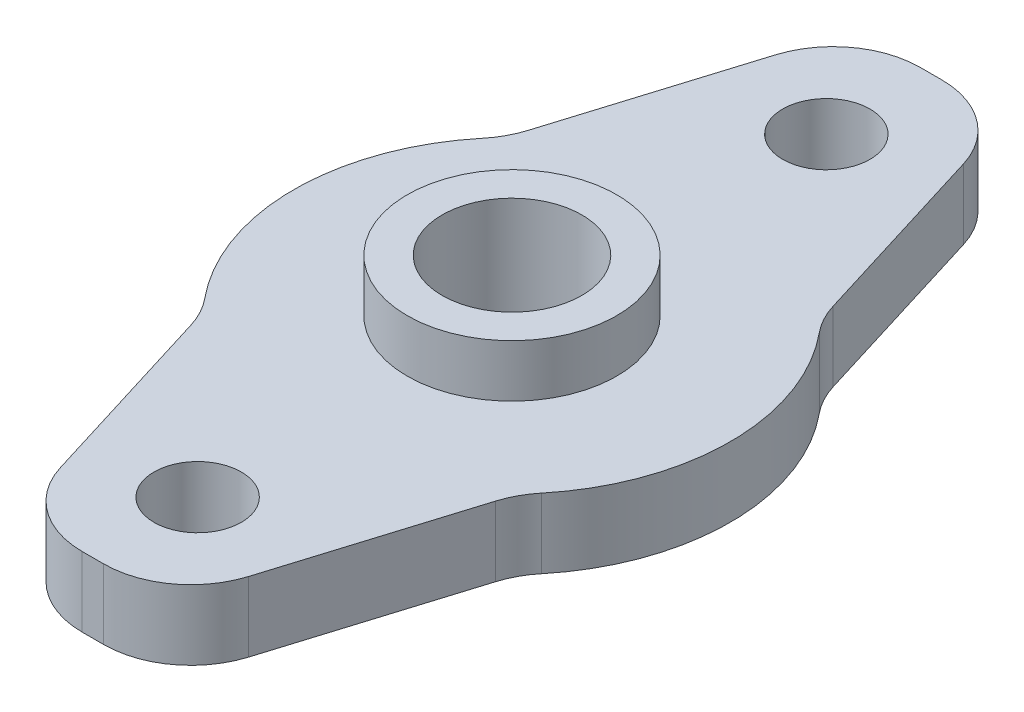
SolidWorks part; units mm, degrees
ref_plane "前视基准面" through (0, 0, 0) normal (0, 0, 1) x (1, 0, 0)
ref_plane "上视基准面" through (0, 0, 0) normal (0, 1, 0) x (1, 0, 0)
ref_plane "右视基准面" through (0, 0, 0) normal (1, 0, 0) x (0, 0, -1)
sketch "草图1" plane through (0, 0, 0) normal (0, 1, 0) x (1, 0, 0)
  line L0 (0, 72.3626) -> (0, -78.1892) construction
  line L1 (-94.3533, 0) -> (86.6472, 0) construction
  line L2 (-94.3533, -18) -> (86.6472, -18) construction
  line L3 (-94.3533, 18) -> (86.6472, 18) construction
  line L4 (-94.3533, -24) -> (86.6472, -24)
  line L5 (-94.3533, 24) -> (86.6472, 24)
  line L6 (-4.306, 24) -> (-9.0423, 8.6306)
  line L7 (4.306, 24) -> (9.0423, 8.6306)
  line L8 (4.306, -24) -> (9.0423, -8.6306)
  line L9 (-4.306, -24) -> (-9.0423, -8.6306)
  circle A0 centre (0, 0) radius 4
  circle A1 centre (0, 18) radius 2.5
  circle A2 centre (0, -18) radius 2.5
  circle A3 centre (0, 0) radius 12.5
  dimension "D1" = 8
  dimension "D4" = 5
  dimension "D5" = 25
  dimension "D2" = 18
  dimension "D3" = 18
  dimension "D6" = 24
  dimension "D7" = 24
extrude "凸台-拉伸1" add sketch "草图1" along normal blind 4 contours A3 L9 L4 L8 A2 | A3 A0 | A3 L7 L5 L6 A1
fillet "圆角1" radius 5 8 edges at (-9.0423, 2, -8.6306) (9.0423, 2, -8.6306) (9.0423, 2, 8.6306) (-9.0423, 2, 8.6306) (-4.306, 2, 24) (4.306, 2, 24) (-4.306, 2, -24) (4.306, 2, -24)
sketch "草图2" plane through (0, 4, 0) normal (0, 1, 0) x (1, 0, 0)
  circle A0 centre (0, 0) radius 6
  circle A1 centre (0, 0) radius 4 construction
  circle A2 centre (0, 0) radius 4
  dimension "D1" = 12
extrude "凸台-拉伸2" add sketch "草图2" along normal blind 3
